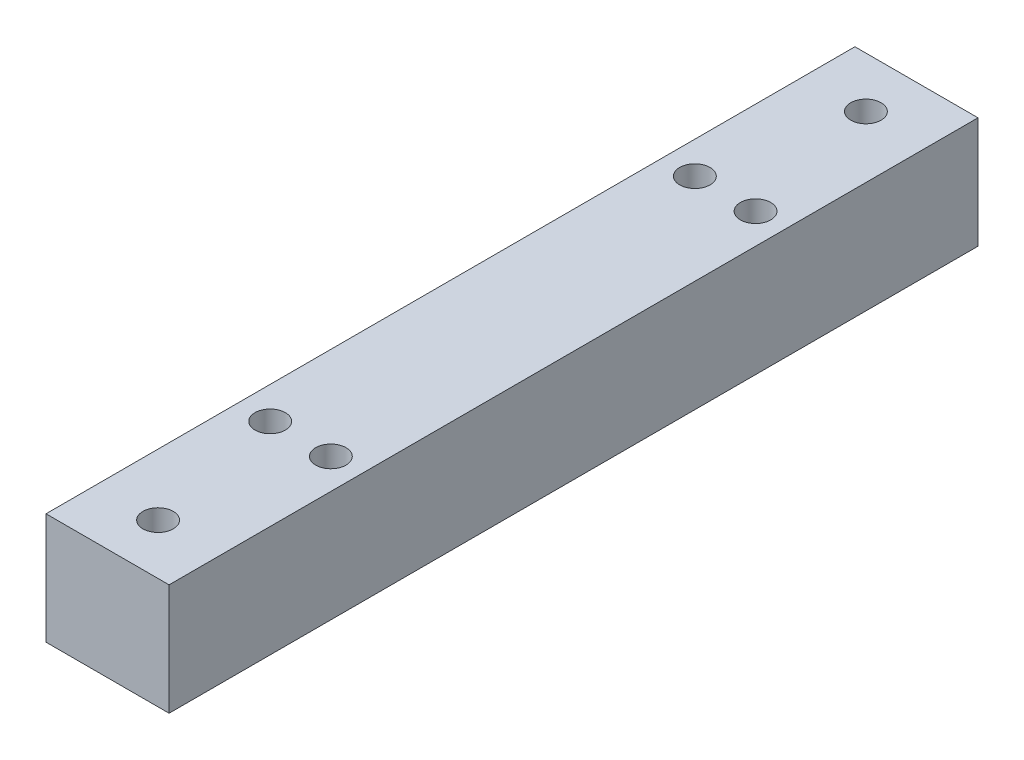
SolidWorks part; units mm, degrees
ref_plane "Front Plane" through (0, 0, 0) normal (0, 0, 1) x (1, 0, 0)
ref_plane "Top Plane" through (0, 0, 0) normal (0, 1, 0) x (1, 0, 0)
ref_plane "Right Plane" through (0, 0, 0) normal (1, 0, 0) x (0, 0, -1)
sketch "Sketch1" plane through (0, 0, 0) normal (0, 0, 1) x (1, 0, 0)
  line L1 (0, 0) -> (12.171, 0)
  line L2 (0, 0) -> (0, 11)
  line L3 (0, 11) -> (12.171, 11)
  line L4 (12.171, 0) -> (12.171, 11)
  dimension "D1" = 12.171
  dimension "D2" = 11
extrude "Boss-Extrude1" add sketch "Sketch1" along normal blind 80
sketch "Sketch2" plane through (0, 11, 0) normal (0, 1, 0) x (1, 0, 0)
  line L0 (0, -80) -> (0, 0) construction
  line L1 (12.171, -80) -> (12.171, 0) construction
  line L2 (12.171, -80) -> (0, -80) construction
  line L3 (12.171, -40) -> (-14.7835, -40) construction
  circle A0 centre (3.17, -61) radius 1.5
  circle A1 centre (9.171, -61) radius 1.5
  circle A2 centre (3.17, -19) radius 1.5
  circle A3 centre (9.171, -19) radius 1.5
  dimension "D1" = 3
  dimension "D2" = 3
  dimension "D3" = 3.17
  dimension "D4" = 3
  dimension "D5" = 19
  dimension "D6" = 19
extrude "Cut-Extrude1" cut sketch "Sketch2" against normal blind 15
sketch "Sketch4" plane through (0, 11, 0) normal (0, 1, 0) x (1, 0, 0)
  line L0 (12.171, -40) -> (-13.027, -40) construction
  line L1 (12.171, -80) -> (12.171, 0) construction
  line L2 (12.171, -80) -> (0, -80) construction
  line L3 (0, -80) -> (0, 0) construction
  circle A0 centre (6.085, -75) radius 1.5
  circle A1 centre (6.085, -5) radius 1.5
  dimension "D1" = 3
  dimension "D2" = 5
  dimension "D3" = 6.085
extrude "Cut-Extrude2" cut sketch "Sketch4" against normal blind 27
